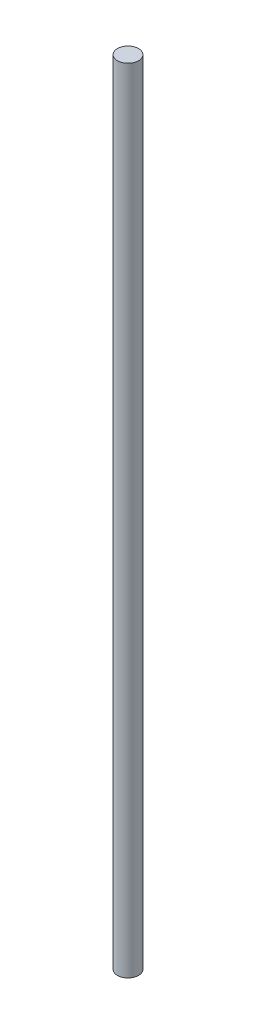
SolidWorks part; units mm, degrees
ref_plane "前视基准面" through (0, 0, 0) normal (0, 0, 1) x (1, 0, 0)
ref_plane "上视基准面" through (0, 0, 0) normal (0, 1, 0) x (1, 0, 0)
ref_plane "右视基准面" through (0, 0, 0) normal (1, 0, 0) x (0, 0, -1)
sketch "草图1" plane through (0, 0, 0) normal (0, 1, 0) x (1, 0, 0)
  circle A0 centre (0, 0) radius 4
extrude "凸台-拉伸1" add sketch "草图1" along normal blind 300
